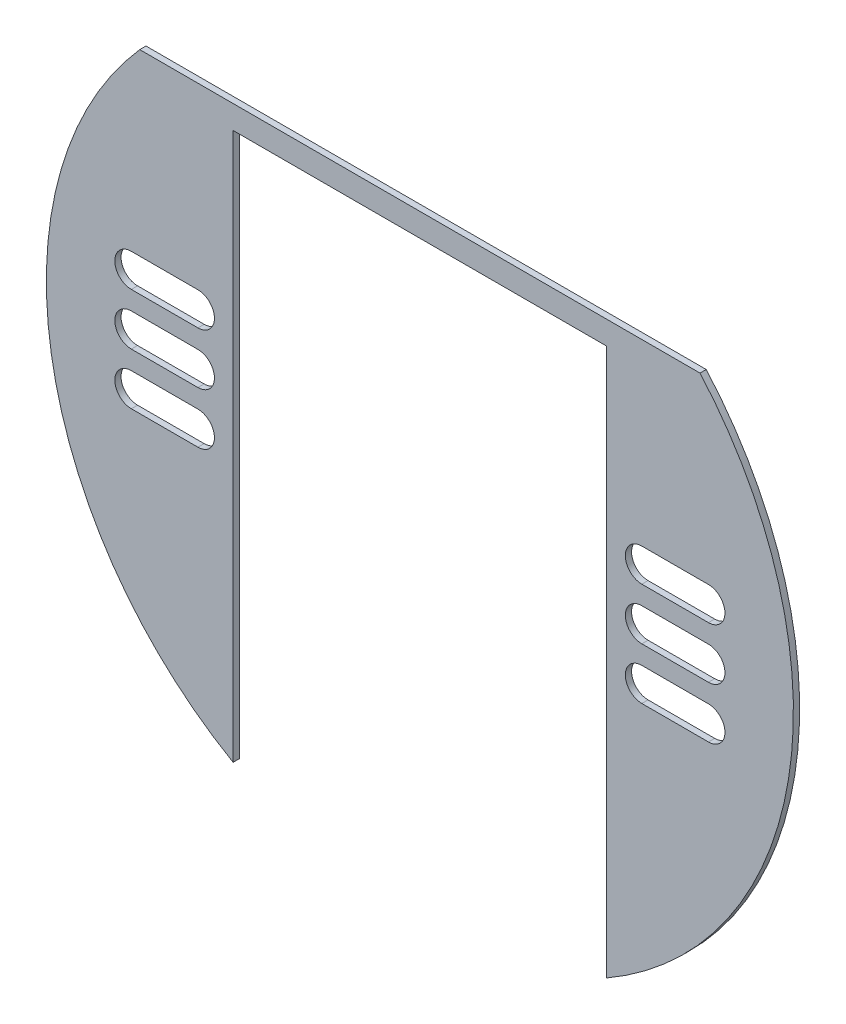
SolidWorks part; units mm, degrees
ref_plane "Front Plane" through (0, 0, 0) normal (0, 0, 1) x (1, 0, 0)
ref_plane "Top Plane" through (0, 0, 0) normal (0, 1, 0) x (1, 0, 0)
ref_plane "Right Plane" through (0, 0, 0) normal (1, 0, 0) x (0, 0, -1)
sketch "Sketch1" plane through (0, 0, 0) normal (0, 0, 1) x (1, 0, 0)
  line L8 (-30, 0) -> (30, 0) construction
  line L9 (-30, -13.1004) -> (-30, -101)
  line L12 (-35.65, -40.7385) -> (-46.35, -40.7385) construction
  line L15 (30, -101) -> (30, -13.1004)
  line L16 (-35.65, -43.3885) -> (-46.35, -43.3885)
  line L17 (-35.65, -38.0885) -> (-46.35, -38.0885)
  line L18 (-35.65, -49.0385) -> (-46.35, -49.0385) construction
  line L21 (-35.65, -51.6885) -> (-46.35, -51.6885)
  line L22 (-35.65, -46.3885) -> (-46.35, -46.3885)
  line L23 (-35.65, -57.3385) -> (-46.35, -57.3385) construction
  line L24 (-35.65, -59.9885) -> (-46.35, -59.9885)
  line L25 (-35.65, -54.6885) -> (-46.35, -54.6885)
  line L26 (46.35, -40.7385) -> (35.65, -40.7385) construction
  line L27 (46.35, -43.3885) -> (35.65, -43.3885)
  line L28 (46.35, -38.0885) -> (35.65, -38.0885)
  line L29 (46.35, -49.0385) -> (35.65, -49.0385) construction
  line L30 (46.35, -51.6885) -> (35.65, -51.6885)
  line L31 (46.35, -46.3885) -> (35.65, -46.3885)
  line L32 (46.35, -57.3385) -> (35.65, -57.3385) construction
  line L33 (46.35, -59.9885) -> (35.65, -59.9885)
  line L34 (46.35, -54.6885) -> (35.65, -54.6885)
  line L35 (-33, -26.5131) -> (-33, -76.1292) construction
  line L36 (-49, -76.1292) -> (-49, -26.5131) construction
  line L37 (33, -26.5131) -> (33, -76.5131) construction
  line L38 (49, -76.5131) -> (49, -26.5131) construction
  line L40 (-45, -9.3522) -> (45, -9.3522)
  line L41 (-30, -13.1004) -> (30, -13.1004)
  arc A4 (-30, -101) -> (-45, -9.3522) centre (0, -49.0385) cw
  arc A5 (-35.65, -43.3885) -> (-35.65, -38.0885) centre (-35.65, -40.7385) ccw
  arc A6 (-46.35, -38.0885) -> (-46.35, -43.3885) centre (-46.35, -40.7385) ccw
  arc A7 (-35.65, -51.6885) -> (-35.65, -46.3885) centre (-35.65, -49.0385) ccw
  arc A8 (-46.35, -46.3885) -> (-46.35, -51.6885) centre (-46.35, -49.0385) ccw
  arc A9 (-35.65, -59.9885) -> (-35.65, -54.6885) centre (-35.65, -57.3385) ccw
  arc A10 (-46.35, -54.6885) -> (-46.35, -59.9885) centre (-46.35, -57.3385) ccw
  arc A11 (46.35, -43.3885) -> (46.35, -38.0885) centre (46.35, -40.7385) ccw
  arc A12 (35.65, -38.0885) -> (35.65, -43.3885) centre (35.65, -40.7385) ccw
  arc A13 (46.35, -51.6885) -> (46.35, -46.3885) centre (46.35, -49.0385) ccw
  arc A14 (35.65, -46.3885) -> (35.65, -51.6885) centre (35.65, -49.0385) ccw
  arc A15 (46.35, -59.9885) -> (46.35, -54.6885) centre (46.35, -57.3385) ccw
  arc A16 (35.65, -54.6885) -> (35.65, -59.9885) centre (35.65, -57.3385) ccw
  arc A17 (45, -9.3522) -> (30, -101) centre (0, -49.0385) cw
  point P5 (-41, -40.7385)
  point P6 (0, 0)
  point P13 (-41, -49.0385)
  point P21 (-41, -57.3385)
  point P29 (41, -40.7385)
  point P36 (41, -49.0385)
  point P43 (41, -57.3385)
  dimension "D4" = 5.3
  dimension "D5" = 5.3
  dimension "D6" = 5.3
  dimension "D8" = 5.3
  dimension "D3" = 60
  dimension "D12" = 49.616
  dimension "D1" = 60
  dimension "D2" = 101
  dimension "D7" = 5.3
  dimension "D9" = 5.3
  dimension "D10" = 3
  dimension "D11" = 3
  dimension "D13" = 16
  dimension "D14" = 3
  dimension "D15" = 3
  dimension "D16" = 16
  dimension "D17" = 50
  dimension "D18" = 24.4869
  dimension "D19" = 3.7482
  dimension "D20" = 90
extrude "Boss-Extrude2" add sketch "Sketch1" along normal blind 1
sketch "Sketch63" plane through (0, 0, 1) normal (0, 0, 1) x (1, 0, 0)
  line L1 (-39.5, -9.3522) -> (39.5, -9.3522)
  line L2 (-39.5, -9.3522) -> (-39.5, -13.1004)
  line L3 (-39.5, -13.1004) -> (39.5, -13.1004)
  line L4 (39.5, -9.3522) -> (39.5, -13.1004)
  point P5 (0, -9.3522)
  dimension "D1" = 79
  dimension "D2" = 3.7482
extrude "Boss-Extrude3" [suppressed] add sketch "Sketch63" against normal blind 40
sketch "Sketch64" [suppressed] plane through (0, -9.3522, 0) normal (0, 1, 0) x (1, 0, 0)
  line L0 (39.5, 39) -> (39.5, 0) construction
  line L1 (-39.5, 39) -> (39.5, 39)
  line L2 (-39.5, 39) -> (-39.5, 35)
  line L3 (-39.5, 35) -> (39.5, 35)
  line L4 (39.5, 39) -> (39.5, 35)
  dimension "D1" = 4
extrude "Boss-Extrude4" [suppressed] add sketch "Sketch64" along normal blind 55
sketch "Sketch65" [suppressed] plane through (0, 0, -35) normal (0, 0, 1) x (1, 0, 0)
  line L0 (39.5, 45.6478) -> (39.5, -9.3522) construction
  line L1 (-39.5, 45.6478) -> (39.5, 45.6478)
  line L2 (-39.5, 45.6478) -> (-39.5, 41.6478)
  line L3 (-39.5, 41.6478) -> (39.5, 41.6478)
  line L4 (39.5, 45.6478) -> (39.5, 41.6478)
  dimension "D1" = 4
extrude "Boss-Extrude5" [suppressed] add sketch "Sketch65" along normal up to surface (36 mm away)
sketch "Sketch66" [suppressed] plane through (0, 45.6478, 0) normal (0, 1, 0) x (1, 0, 0)
  line L0 (-27.275, 39) -> (27.275, 39) construction
  line L1 (39.5, 39) -> (-39.5, 39) construction
  line L4 (-39.5, 39) -> (-27.275, 39)
  line L5 (27.275, 39) -> (39.5, 39)
  line L6 (39.5, 39) -> (39.5, -1)
  line L8 (-36.5, 0) -> (-39.5, 0)
  line L9 (-39.5, 0) -> (-39.5, 39)
  line L10 (39.5, 39) -> (39.5, 0)
  line L11 (39.5, 0) -> (36.5, 0)
  line L13 (-36.5, 0) -> (-36.5, 10.3305)
  line L14 (-36.5, 10.3305) -> (-27.275, 39)
  line L15 (36.5, 0) -> (36.5, 10.3547)
  line L16 (36.5, 10.3547) -> (27.275, 39)
  point P4 (0, 39)
  dimension "D1" = 54.55
  dimension "D2" = 3
  dimension "D3" = 3
  dimension "D4" = 162.163
  dimension "D5" = 162.149
extrude "Cut-Extrude6" [suppressed] cut sketch "Sketch66" against normal blind 65
sketch "Sketch67" [suppressed] plane through (0, 45.6478, 0) normal (0, 1, 0) x (1, 0, 0)
  line L0 (-27.275, 39) -> (-24.6488, 39)
  line L1 (27.275, 39) -> (-27.275, 39) construction
  line L3 (-34, 0) -> (-36.5, 0)
  line L6 (36.5, 0) -> (34, 0)
  line L8 (24.6486, 39) -> (27.275, 39)
  line L9 (27.275, 39) -> (36.5, 10.3547)
  line L10 (36.5, 10.3547) -> (36.5, 0)
  line L11 (34, 0) -> (34, 9.9621)
  line L12 (34, 9.9621) -> (24.6486, 39)
  line L13 (-36.5, 0) -> (-36.5, 10.3305)
  line L14 (-36.5, 10.3305) -> (-27.275, 39)
  line L15 (-24.6488, 39) -> (-34, 9.9382)
  line L16 (-34, 9.9382) -> (-34, 0)
  dimension "D1" = 2.5
  dimension "D2" = 2.5
  dimension "D3" = 2.5
  dimension "D4" = 2.5
extrude "Boss-Extrude6" [suppressed] add sketch "Sketch67" against normal up to vertex
fillet "Fillet1" [suppressed] radius 10
fillet "Fillet2" [suppressed] radius 5
sketch "Sketch68" [suppressed] plane through (0, 45.6478, 0) normal (0, 1, 0) x (1, 0, 0)
  line L0 (-39.5, -1) -> (-39.5, 10)
  line L1 (-39.5, 10) -> (39.5, 10)
  line L2 (39.5, 10) -> (39.5, -1)
  line L3 (39.5, -1) -> (-39.5, -1)
  dimension "D1" = 11
extrude "Cut-Extrude7" [suppressed] cut sketch "Sketch68" against normal blind 41
sketch "Sketch69" [suppressed] plane through (0, 0, -10) normal (0, 0, 1) x (1, 0, 0)
  line L1 (-26.1014, 45.6478) -> (26.1085, 45.6478)
  line L2 (-26.1014, 45.6478) -> (-26.1014, 41.6478)
  line L3 (-26.1014, 41.6478) -> (26.1085, 41.6478)
  line L4 (26.1085, 45.6478) -> (26.1085, 41.6478)
  line L5 (45, -9.3522) -> (-45, -9.3522) construction
  dimension "D1" = 4
  dimension "D4" = 51
extrude "Boss-Extrude7" [suppressed] add sketch "Sketch69" along normal blind 20
sketch "Sketch70" [suppressed] plane through (0, 0, 0) normal (0, 1, 0) x (1, 0, 0)
  line L0 (34.3048, 0) -> (45, 0) construction
  line L1 (-66.0838, 0) -> (60, 0)
  line L2 (-66.0838, 0) -> (-66.0838, -10)
  line L4 (60, 0) -> (60, -10)
  line L5 (60, -1) -> (60, 0) construction
  line L6 (60, -10) -> (-66.0838, -10)
  dimension "D1" = 10
  dimension "D2" = 126.0838
extrude "Cut-Extrude8" [suppressed] cut sketch "Sketch70" against normal blind 129
fillet "Fillet4" [suppressed] radius 3
